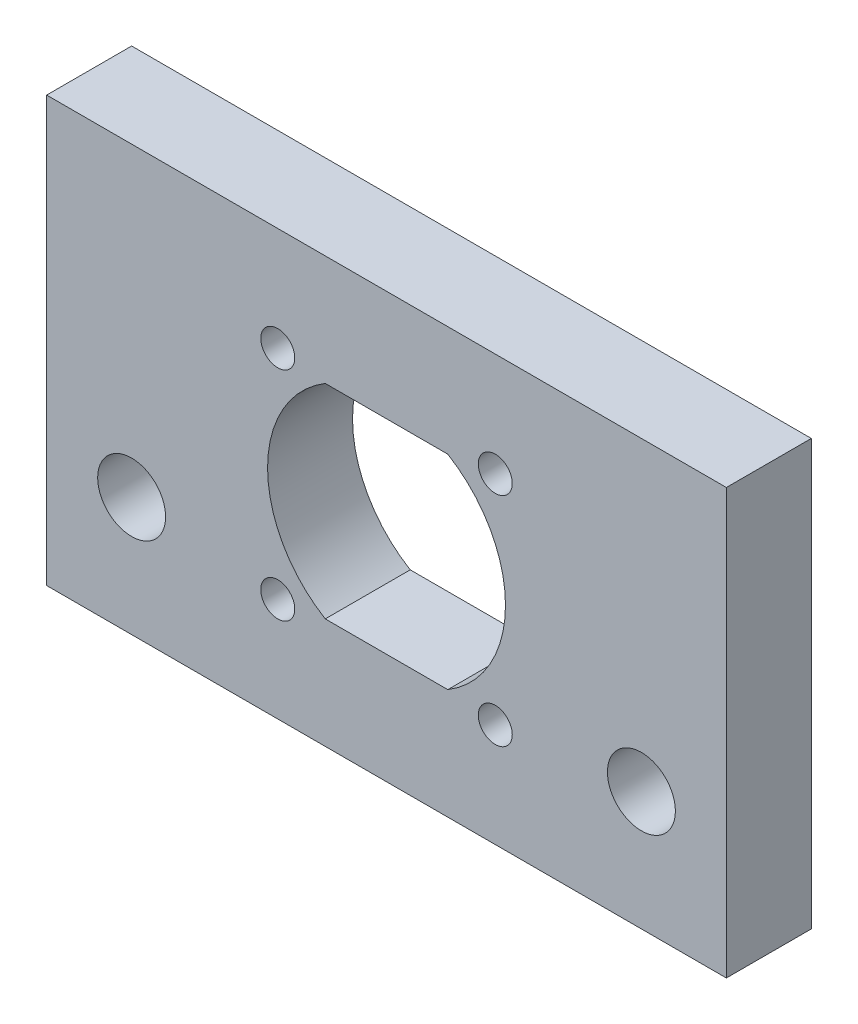
SolidWorks part; units mm, degrees
ref_plane "Front Plane" through (0, 0, 0) normal (0, 0, 1) x (1, 0, 0)
ref_plane "Top Plane" through (0, 0, 0) normal (0, 1, 0) x (1, 0, 0)
ref_plane "Right Plane" through (0, 0, 0) normal (1, 0, 0) x (0, 0, -1)
sketch "Sketch1" plane through (0, 0, 0) normal (0, 0, 1) x (1, 0, 0)
  line L0 (0, 0) -> (-10.2726, 0) construction
  line L1 (-20, 12.5) -> (20, 12.5)
  line L2 (-20, 12.5) -> (-20, -12.5)
  line L3 (-20, -12.5) -> (20, -12.5)
  line L4 (20, 12.5) -> (20, -12.5)
  line L5 (-20, 12.5) -> (20, -12.5) construction
  line L6 (-20, -12.5) -> (20, 12.5) construction
  line L7 (-3.6056, 6) -> (3.6056, 6)
  line L9 (-3.6056, -6) -> (3.6056, -6)
  line L11 (-3.6056, 6) -> (3.6056, -6) construction
  line L12 (-3.6056, -6) -> (3.6056, 6) construction
  line L13 (0, 0) -> (5.8199, 9.3118) construction
  line L14 (0, 0) -> (0, 9.2066) construction
  line L16 (-22.9778, -7.1521) -> (-22.9778, -6.4) construction
  arc A1 (-3.6056, 6) -> (-3.6056, -6) centre (0, 0) ccw
  arc A2 (3.6056, -6) -> (3.6056, 6) centre (0, 0) ccw
  circle A10 centre (15, -5.5) radius 2
  circle A12 centre (-6.4, 6.4) radius 1
  circle A15 centre (-15, -5.5) radius 2
  circle A16 centre (6.4, 6.4) radius 1
  circle A17 centre (6.4, -6.4) radius 1
  circle A18 centre (-6.4, -6.4) radius 1
  point P0 (0, 0)
  point P21 (0, 0)
  point P22 (0, 0)
  dimension "D3" = 14
  dimension "D5" = 2
  dimension "D6" = 6.4
  dimension "D9" = 4
  dimension "D12" = 22.9778
  dimension "D7" = 6.4
  dimension "D1" = 40
  dimension "D2" = 25
  dimension "D4" = 12
  dimension "D10" = 5.5
  dimension "D11" = 15
extrude "Boss-Extrude1" add sketch "Sketch1" along normal blind 5
